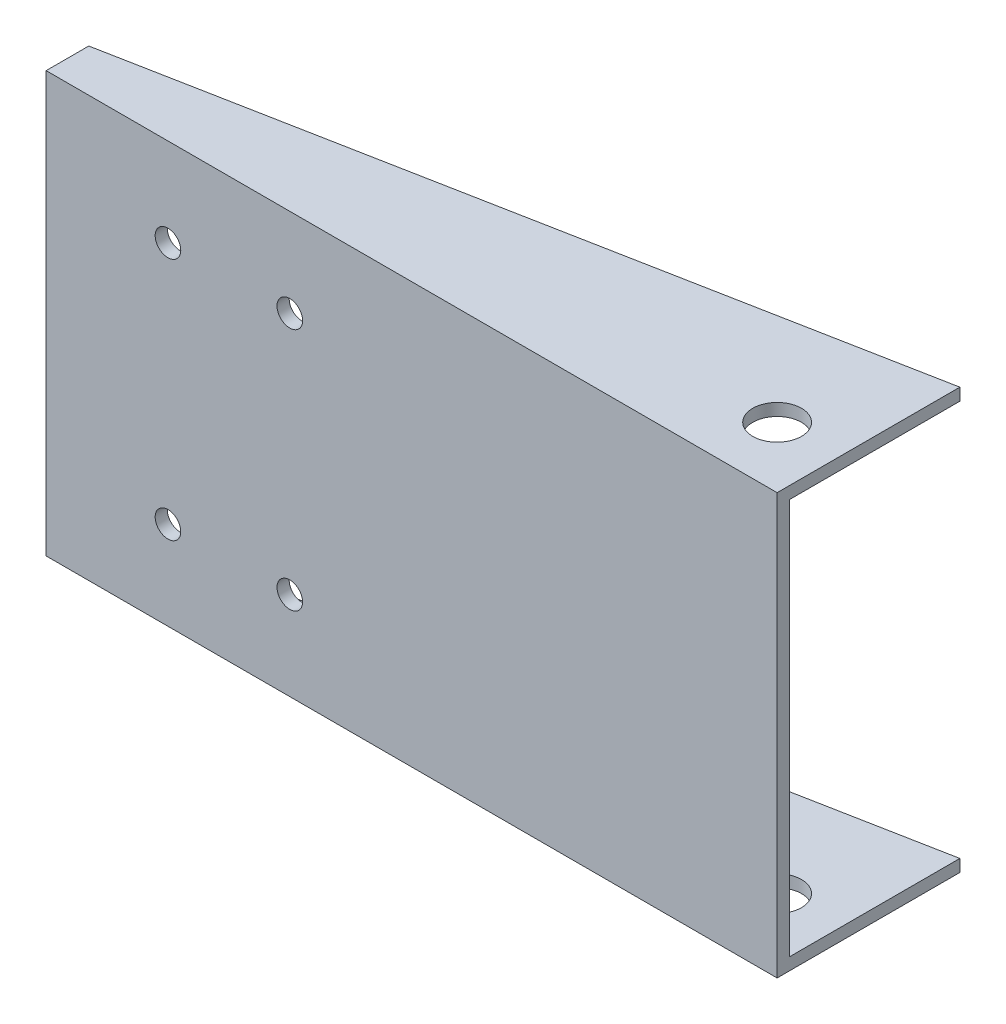
SolidWorks part; units mm, degrees
ref_plane "前视基准面" through (0, 0, 0) normal (0, 0, 1) x (1, 0, 0)
ref_plane "上视基准面" through (0, 0, 0) normal (0, 1, 0) x (1, 0, 0)
ref_plane "右视基准面" through (0, 0, 0) normal (1, 0, 0) x (0, 0, -1)
sketch "草图1" plane through (0, 0, 0) normal (0, 0, 1) x (1, 0, 0)
  line L0 (-35.0053, 28.2783) -> (84.9947, 28.2783)
  line L1 (84.9947, 28.2783) -> (84.9947, 93.2783)
  line L2 (84.9947, 93.2783) -> (-35.0053, 93.2783)
  line L3 (-35.0053, 93.2783) -> (-35.0053, 28.2783)
  dimension "D1" = 120
  dimension "D2" = 65
extrude "凸台-拉伸1" add sketch "草图1" along normal blind 2
sketch "草图2" plane through (0, 28.2783, 0) normal (0, -1, 0) x (1, 0, 0)
  line L0 (-35.0053, 2) -> (-35.0053, 0)
  line L1 (-35.0053, 0) -> (-35.0053, -5)
  line L2 (-35.0053, 2) -> (84.9947, 2)
  line L3 (-35.0053, 2) -> (84.9947, 2) construction
  line L4 (84.9947, 2) -> (84.9947, -28)
  line L5 (84.9947, -28) -> (-35.0053, -5)
  dimension "D1" = 5
  dimension "D2" = 30
extrude "凸台-拉伸2" add sketch "草图2" along normal blind 2
ref_plane "基准面1" through (0, 60.7783, 0) normal (0, 1, 0) x (1, 0, 0)
mirror "镜向1" about plane through (0, 60.7783, 0) normal (0, 1, 0) of "凸台-拉伸2"
sketch "草图3" plane through (0, 0, 2) normal (0, 0, 1) x (1, 0, 0)
  line L0 (-89.0805, 60.7783) -> (84.9947, 60.7783) construction
  line L1 (55, 60.7783) -> (-55, 60.7783) construction
  line L2 (84.9947, 26.2783) -> (84.9947, 95.2783) construction
  line L3 (84.9947, 60.7783) -> (84.9947, 80.7783) construction
  line L4 (84.9947, 80.7783) -> (-15.0053, 80.7783) construction
  line L5 (-15.0053, 80.7783) -> (4.9947, 80.7783) construction
  circle A0 centre (-15.0053, 80.7783) radius 2.1
  circle A1 centre (4.9947, 80.7783) radius 2.1
  circle A2 centre (-15.0053, 40.7783) radius 2.1
  circle A3 centre (4.9947, 40.7783) radius 2.1
  dimension "D3" = 4.2
  dimension "D5" = 4.2
  dimension "D1" = 20
  dimension "D2" = 100
  dimension "D4" = 20
extrude "切除-拉伸1" cut sketch "草图3" against normal blind 2
sketch "草图4" plane through (0, 26.2783, 0) normal (0, -1, 0) x (-1, 0, 0)
  line L0 (-84.9947, -2) -> (-84.9947, 8) construction
  line L1 (-84.9947, 28) -> (-84.9947, -2) construction
  line L2 (-84.9947, 8) -> (-74.9947, 8) construction
  circle A0 centre (-74.9947, 8) radius 4
  dimension "D3" = 8
  dimension "D1" = 10
  dimension "D2" = 10
extrude "切除-拉伸2" cut sketch "草图4" against normal blind 70
